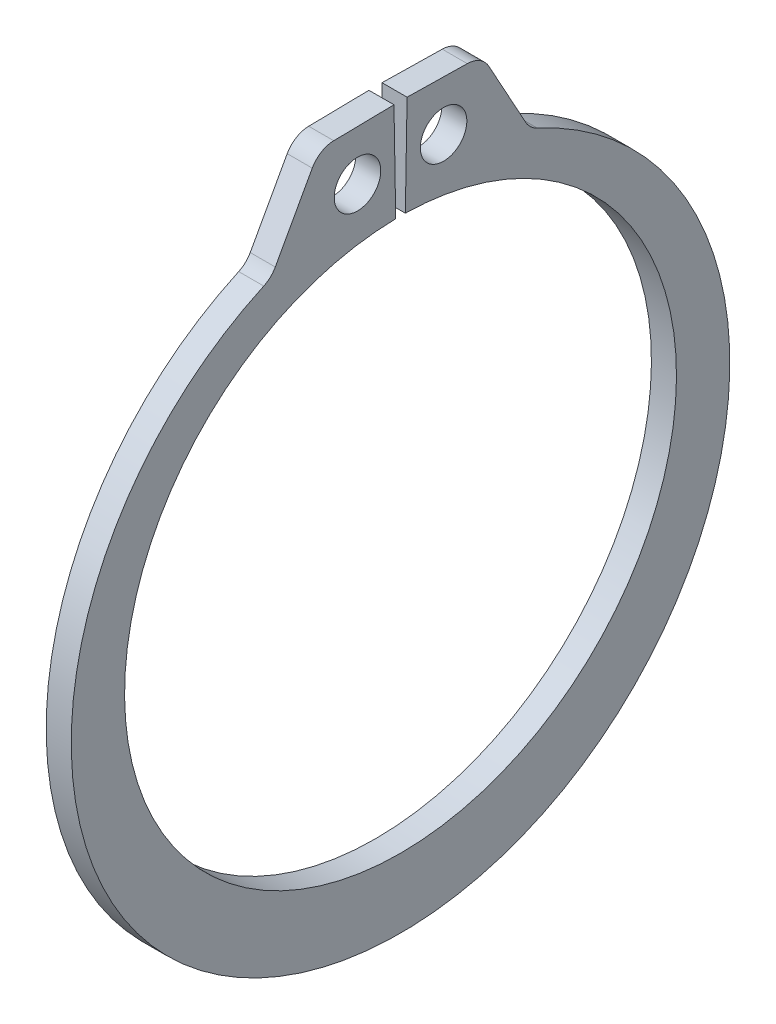
SolidWorks part; units mm, degrees
material "Cast Carbon Steel"
ref_plane "Front" through (0, 0, 0) normal (0, 0, 1) x (1, 0, 0)
ref_plane "Top" through (0, 0, 0) normal (0, 1, 0) x (1, 0, 0)
ref_plane "Right" through (0, 0, 0) normal (1, 0, 0) x (0, 0, -1)
sketch "Sketch1" plane through (0, 0, 0) normal (1, 0, 0) x (0, 0, -1)
  line L0 (0, 0) -> (0, 11.7475) construction
  line L1 (-0.205, 11.7457) -> (-0.2791, 15.9869)
  line L2 (0.2791, 15.9869) -> (3.4599, 15.9313)
  line L3 (3.4599, 15.9313) -> (5.5053, 12.2152)
  line L4 (0.205, 11.7457) -> (0.2791, 15.9869)
  line L5 (-0.2791, 15.9869) -> (-3.4599, 15.9313)
  line L6 (-3.4599, 15.9313) -> (-5.5053, 12.2152)
  line L7 (-5.5053, 12.2152) -> (-4.8269, 10.71) construction
  line L8 (5.5053, 12.2152) -> (4.8269, 10.71) construction
  line L9 (0, -11.7475) -> (0, -14.6939) construction
  line L10 (-3.4599, 15.9313) -> (-0.205, 11.7457) construction
  line L11 (0, 11.7475) -> (0, 15.9893) construction
  line L12 (-11.7475, 0) -> (11.7475, 0) construction
  circle A0 centre (0, 0) radius 11.7475 construction
  arc A1 (-0.205, 11.7457) -> (0.205, 11.7457) centre (0, 0) ccw
  circle A3 centre (0, 0) radius 17.526 construction
  circle A4 centre (-1.8325, 13.8385) radius 0.9906
  circle A5 centre (1.8325, 13.8385) radius 0.9906
  arc A6 (-5.5053, 12.2152) -> (5.5053, 12.2152) centre (0, -0.6762) ccw
  point P0 (0, -14.6939)
  dimension "A" = 23.495
  dimension "Hole" = 1.9812
  dimension "Smin" = 1.651
  dimension "H" = 4.2418
  dimension "D2" = 3.1813
  dimension "Angle" = 1
extrude "Extrude1" add sketch "Sketch1" along normal mid plane 1.0668
fillet "Fillet1" radius 1.0668 4 edges at (0, 12.2152, 5.5053) (0, 12.2152, -5.5053) (0, 15.9313, 3.4599) (0, 15.9313, -3.4599)
sketch "Sketch2" plane through (0, 0, 0) normal (0, 0, 1) x (1, 0, 0)
  line L0 (-5.9182, 0) -> (15.4178, 0)
  line L1 (15.4178, 0) -> (15.4178, -12.7)
  line L2 (-5.9182, 0) -> (-5.9182, -11.938)
  line L3 (15.4178, -12.7) -> (0.5842, -12.7)
  line L4 (0.5842, -12.7) -> (0.5842, -11.938)
  line L5 (0.5842, -11.938) -> (-0.5842, -11.938)
  line L6 (-0.5842, -11.938) -> (-0.5842, -12.7)
  line L7 (-0.5842, -12.7) -> (-5.9182, -12.7) construction
  line L8 (-5.9182, -12.7) -> (-5.9182, 0) construction
  line L9 (15.4178, 0) -> (76.391, 0) construction
  line L10 (-5.9182, -11.938) -> (-5.1562, -12.7)
  line L11 (-5.1562, -12.7) -> (-0.5842, -12.7)
  point P10 (0, -11.938)
  dimension "D2" = 21.336
  dimension "D3" = 5.334
  dimension "D1" = 45
revolve "Revolve1" [suppressed] add sketch "Sketch2" angle 360 about L9
delete or keep bodies "Body-Delete1" [suppressed] type delete bodies bodies 122
equation "\"D2@Sketch2\" = \"D1@Extrude1\"*20"
equation "\"D3@Sketch2\" = \"D2@Sketch2\"/4"
equation "\"D2@Sketch1\" = \"H@Sketch1\"*.75"
equation "\"D1@Fillet1\" = \"D1@Extrude1\""
